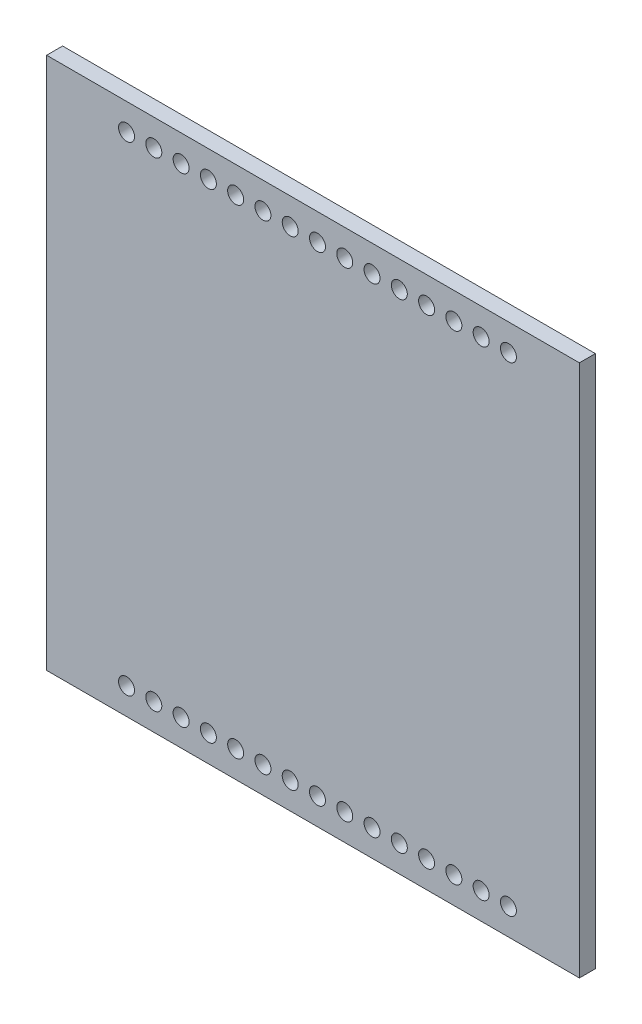
SolidWorks part; units mm, degrees
ref_plane "Front Plane" through (0, 0, 0) normal (0, 0, 1) x (1, 0, 0)
ref_plane "Top Plane" through (0, 0, 0) normal (0, 1, 0) x (1, 0, 0)
ref_plane "Right Plane" through (0, 0, 0) normal (1, 0, 0) x (0, 0, -1)
sketch "Sketch1" plane through (0, 0, 0) normal (0, 0, 1) x (1, 0, 0)
  line L1 (25, -25) -> (-25, -25)
  line L2 (25, -25) -> (25, 25)
  line L3 (25, 25) -> (-25, 25)
  line L4 (-25, -25) -> (-25, 25)
  line L5 (25, -25) -> (-25, 25) construction
  line L6 (25, 25) -> (-25, -25) construction
  point P0 (0, 0)
  dimension "D1" = 50
  dimension "D2" = 50
extrude "Boss-Extrude1" add sketch "Sketch1" along normal blind 1.5
sketch "Sketch2" plane through (0, 0, 1.5) normal (0, 0, 1) x (1, 0, 0)
  line L0 (-25, -25) -> (25, -25) construction
  line L1 (-25, 25) -> (-25, -25) construction
  line L2 (0, 0) -> (-14.94, 0) construction
  circle A0 centre (-17.5, -22.5) radius 0.75
  circle A1 centre (-14.94, -22.5) radius 0.75
  circle A2 centre (-12.38, -22.5) radius 0.75
  circle A3 centre (-9.82, -22.5) radius 0.75
  circle A4 centre (-7.26, -22.5) radius 0.75
  circle A5 centre (-4.7, -22.5) radius 0.75
  circle A6 centre (-2.14, -22.5) radius 0.75
  circle A7 centre (0.42, -22.5) radius 0.75
  circle A8 centre (2.98, -22.5) radius 0.75
  circle A9 centre (5.54, -22.5) radius 0.75
  circle A10 centre (8.1, -22.5) radius 0.75
  circle A11 centre (10.66, -22.5) radius 0.75
  circle A12 centre (13.22, -22.5) radius 0.75
  circle A13 centre (15.78, -22.5) radius 0.75
  circle A14 centre (18.34, -22.5) radius 0.75
  circle A15 centre (18.34, 22.5) radius 0.75
  circle A16 centre (15.78, 22.5) radius 0.75
  circle A17 centre (13.22, 22.5) radius 0.75
  circle A18 centre (10.66, 22.5) radius 0.75
  circle A19 centre (8.1, 22.5) radius 0.75
  circle A20 centre (5.54, 22.5) radius 0.75
  circle A21 centre (2.98, 22.5) radius 0.75
  circle A22 centre (0.42, 22.5) radius 0.75
  circle A23 centre (-2.14, 22.5) radius 0.75
  circle A24 centre (-4.7, 22.5) radius 0.75
  circle A25 centre (-7.26, 22.5) radius 0.75
  circle A26 centre (-9.82, 22.5) radius 0.75
  circle A27 centre (-12.38, 22.5) radius 0.75
  circle A28 centre (-14.94, 22.5) radius 0.75
  circle A29 centre (-17.5, 22.5) radius 0.75
  dimension "D1" = 1.5
  dimension "D3" = 2.5
  dimension "D4" = 7.5
  dimension "D2" = 15
extrude "Cut-Extrude1" cut sketch "Sketch2" against normal through all
